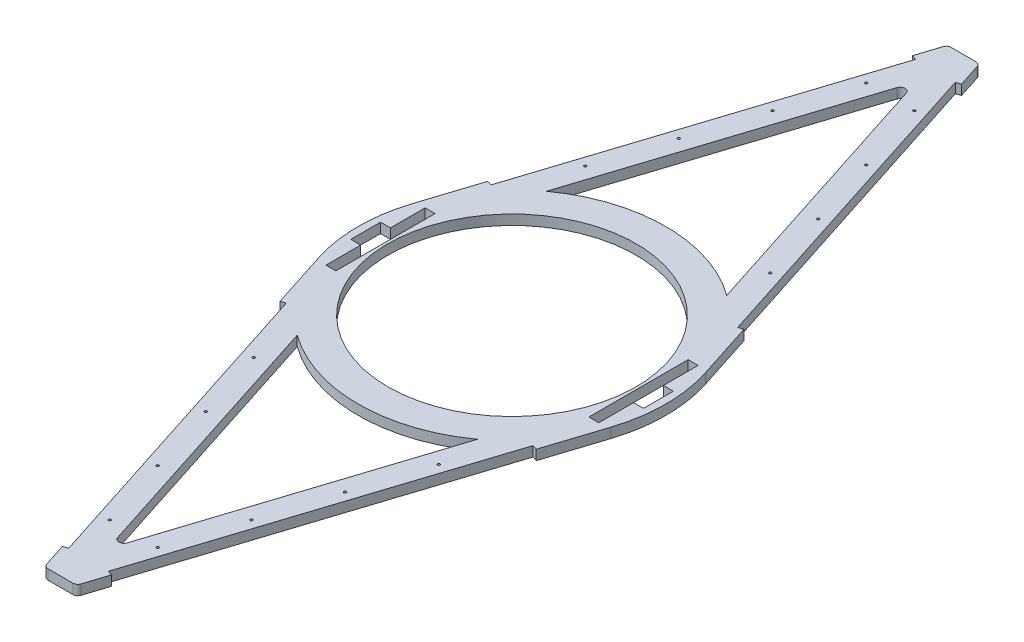
SolidWorks part; units mm, degrees
ref_plane "Front Plane" through (0, 0, 0) normal (0, 0, 1) x (1, 0, 0)
ref_plane "Top Plane" through (0, 0, 0) normal (0, 1, 0) x (1, 0, 0)
ref_plane "Right Plane" through (0, 0, 0) normal (1, 0, 0) x (0, 0, -1)
sketch "Sketch2" plane through (0, 0, 0) normal (0, 1, 0) x (1, 0, 0)
  line L0 (-295.0403, 95.1378) -> (-34.5174, 903.069)
  line L1 (-25, 910) -> (25, 910)
  line L2 (0, 0) -> (0, 979.251) construction
  line L3 (-181.6808, 251.1814) -> (-9.5174, 785.0928)
  line L4 (295.0403, 95.1378) -> (32.2825, 910)
  line L5 (181.6808, 251.1814) -> (9.5174, 785.0928)
  line L6 (0, 912.3611) -> (-253.9796, 124.7221) construction
  line L7 (0, 912.3611) -> (253.9796, 124.7221) construction
  line L8 (-638.4186, 0) -> (595.6196, 0) construction
  line L9 (181.6808, -251.1814) -> (9.5174, -785.0928)
  line L10 (295.0403, -95.1378) -> (32.2825, -910)
  line L11 (-181.6808, -251.1814) -> (-9.5174, -785.0928)
  line L12 (-25, -910) -> (25, -910)
  line L13 (-295.0403, -95.1378) -> (-34.5174, -903.069)
  circle A0 centre (0, 0) radius 250 construction
  arc A1 (181.6808, 251.1814) -> (-181.6808, 251.1814) centre (0, 0) ccw
  arc A2 (-9.5174, 785.0928) -> (9.5174, 785.0928) centre (0, 782.0238) cw
  arc A3 (-295.0403, 95.1378) -> (-295.0403, -95.1378) centre (0, 0) ccw
  arc A4 (-25, 910) -> (-34.5174, 903.069) centre (-25, 900) ccw
  arc A5 (25, 910) -> (34.5174, 903.069) centre (25, 900) cw
  circle A6 centre (-186.4767, 334.0614) radius 2.5
  circle A7 centre (-140.4423, 476.8229) radius 2.5
  circle A8 centre (-94.4079, 619.5843) radius 2.5
  circle A9 centre (-48.3735, 762.3458) radius 2.5
  circle A10 centre (48.3735, 762.3458) radius 2.5
  circle A11 centre (94.4079, 619.5843) radius 2.5
  circle A12 centre (140.4423, 476.8229) radius 2.5
  circle A13 centre (186.4767, 334.0614) radius 2.5
  circle A14 centre (0, 0) radius 250
  circle A15 centre (186.4767, -334.0614) radius 2.5
  circle A16 centre (140.4423, -476.8229) radius 2.5
  circle A17 centre (94.4079, -619.5843) radius 2.5
  circle A18 centre (48.3735, -762.3458) radius 2.5
  circle A19 centre (-48.3735, -762.3458) radius 2.5
  circle A20 centre (-94.4079, -619.5843) radius 2.5
  circle A21 centre (-140.4423, -476.8229) radius 2.5
  circle A22 centre (-186.4767, -334.0614) radius 2.5
  arc A23 (25, -910) -> (34.5174, -903.069) centre (25, -900) ccw
  arc A24 (-25, -910) -> (-34.5174, -903.069) centre (-25, -900) cw
  arc A25 (-9.5174, -785.0928) -> (9.5174, -785.0928) centre (0, -782.0238) ccw
  arc A26 (181.6808, -251.1814) -> (-181.6808, -251.1814) centre (0, 0) cw
  arc A27 (-181.6808, -251.1814) -> (181.6808, -251.1814) centre (0, 0) ccw
  arc A28 (295.0403, -95.1378) -> (295.0403, 95.1378) centre (0, 0) ccw
  point P15 (0, 814.6081)
  point P17 (-32.2825, 910)
  point P21 (0, 910)
  point P70 (0, -910)
  dimension "D1" = 500
  dimension "D2" = 10
  dimension "D3" = 10
  dimension "D4" = 5
  dimension "D10" = 500
  dimension "D5" = 150
  dimension "D6" = 150
  dimension "D7" = 150
  dimension "D8" = 60
  dimension "D9" = 910
  dimension "D11" = 50
  dimension "D12" = 30
extrude "Boss-Extrude1" add sketch "Sketch2" along normal blind 20 contours A5 L1 A4 L0 A3 L4 A12 A10 A9 A8 A7 A6 A0 L3 A2 L5 A1 A11 A13
sketch "Sketch3" plane through (0, 20, 0) normal (0, 1, 0) x (1, 0, 0)
  line L0 (-49.5235, -856.5322) -> (-40.0061, -853.4632)
  line L1 (-295.0403, -95.1378) -> (-34.5174, -903.069) construction
  line L2 (-40.0061, -853.4632) -> (-285.5229, -92.0688) construction
  line L3 (-49.5235, -856.5322) -> (-295.0403, -95.1378) construction
  line L4 (-536.968, 0) -> (576.6024, 0) construction
  line L5 (-49.5235, 856.5322) -> (-40.0061, 853.4632)
  line L6 (-49.5235, 856.5322) -> (-295.0403, 95.1378) construction
  line L7 (-40.0061, 853.4632) -> (-285.5229, 92.0688) construction
  line L8 (49.5235, 856.5322) -> (40.0061, 853.4632)
  line L9 (49.5235, -856.5322) -> (40.0061, -853.4632)
  line L10 (40.0061, 853.4632) -> (285.5229, 92.0688) construction
  line L11 (49.5235, 856.5322) -> (295.0403, 95.1378) construction
  line L12 (49.5235, -856.5322) -> (295.0403, -95.1378) construction
  line L13 (40.0061, -853.4632) -> (285.5229, -92.0688) construction
  line L14 (-248.6954, 206.278) -> (-258.2128, 209.3469)
  line L15 (248.6954, -206.278) -> (258.2128, -209.3469)
  line L16 (248.6954, 206.278) -> (258.2128, 209.3469)
  line L17 (-258.2128, -209.3469) -> (-49.5235, -856.5322)
  line L18 (-248.6954, -206.278) -> (-258.2128, -209.3469)
  line L19 (-40.0061, -853.4632) -> (-248.6954, -206.278)
  line L20 (40.0061, -853.4632) -> (248.6954, -206.278)
  line L21 (258.2128, -209.3469) -> (49.5235, -856.5322)
  line L22 (258.2128, 209.3469) -> (49.5235, 856.5322)
  line L23 (40.0061, 853.4632) -> (248.6954, 206.278)
  line L24 (-40.0061, 853.4632) -> (-248.6954, 206.278)
  line L25 (-258.2128, 209.3469) -> (-49.5235, 856.5322)
  line L41 (0, 1098.112) -> (0, -1215.3687) construction
  arc A0 (285.5229, 92.0688) -> (285.5229, -92.0688) centre (0, 0) cw construction
  arc A1 (-295.0403, 95.1378) -> (-295.0403, -95.1378) centre (0, 0) ccw construction
  arc A2 (-285.5229, 92.0688) -> (-285.5229, -92.0688) centre (0, 0) ccw construction
  arc A3 (295.0403, 95.1378) -> (295.0403, -95.1378) centre (0, 0) cw construction
  dimension "D1" = 800
  dimension "D2" = 10
  dimension "D3" = 680
extrude "Cut-Extrude4" cut sketch "Sketch3" against normal through all contours L0 L19 L18 L17 | L5 L24 L14 L25 | L8 L23 L16 L22 | L9 L20 L15 L21
sketch "Sketch4" plane through (0, 20, 0) normal (0, 1, 0) x (1, 0, 0)
  line L0 (0, 0) -> (-550, 0) construction
  line L1 (-255, -100) -> (-255, 100)
  line L2 (-255, 100) -> (-275, 100)
  line L3 (-275, 100) -> (-275, -100) construction
  line L4 (-275, 30) -> (-295, 30)
  line L5 (-295, 30) -> (-295, -30)
  line L6 (-275, 30) -> (-275, 100)
  line L7 (-275, -30) -> (-275, -100)
  line L8 (-275, -30) -> (-295, -30)
  line L9 (-255, -100) -> (-275, -100)
  line L10 (0, 0) -> (0, 506.9475) construction
  line L11 (275, 100) -> (275, -100) construction
  line L12 (255, -100) -> (275, -100)
  line L13 (275, -30) -> (295, -30)
  line L14 (275, -30) -> (275, -100)
  line L15 (275, 30) -> (275, 100)
  line L16 (295, 30) -> (295, -30)
  line L17 (275, 30) -> (295, 30)
  line L18 (255, 100) -> (275, 100)
  line L19 (255, -100) -> (255, 100)
  circle A1 centre (0, 0) radius 275 construction
  point P13 (-275, 0)
  point P15 (-295, 0)
  point P16 (-255, 0)
  point P25 (255, 0)
  point P26 (295, 0)
  point P27 (275, 0)
  dimension "D4" = 550
  dimension "D1" = 20
  dimension "D2" = 20
  dimension "D3" = 30
  dimension "D5" = 200
extrude "Cut-Extrude5" cut sketch "Sketch4" against normal through all
